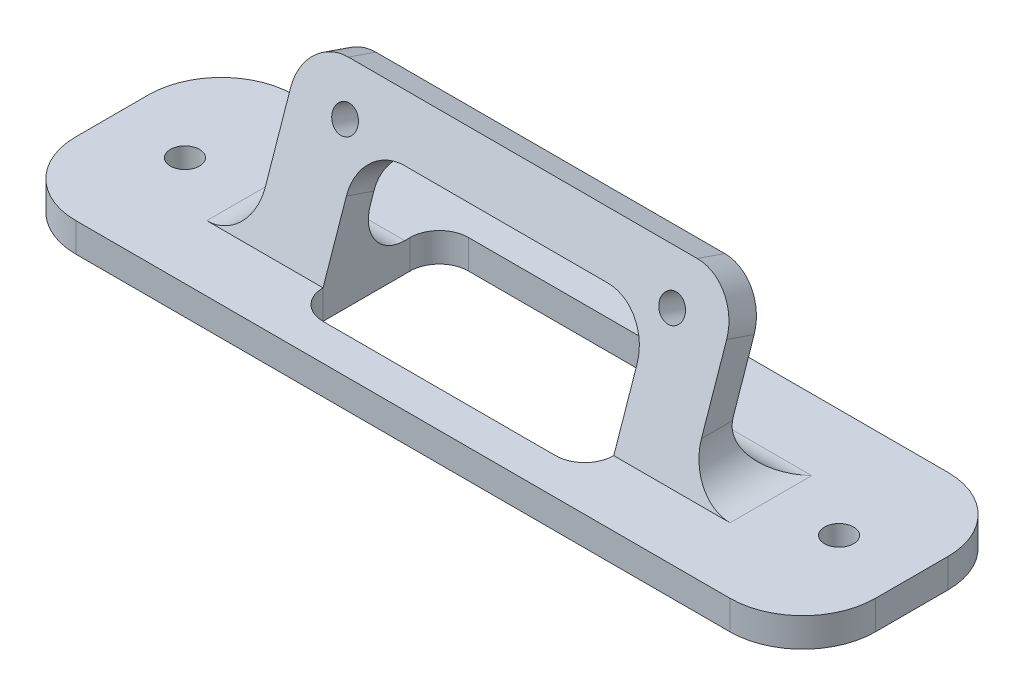
SolidWorks part; units mm, degrees
ref_plane "Plan de face" through (0, 0, 0) normal (0, 0, 1) x (1, 0, 0)
ref_plane "Plan de dessus" through (0, 0, 0) normal (0, 1, 0) x (1, 0, 0)
ref_plane "Plan de droite" through (0, 0, 0) normal (1, 0, 0) x (0, 0, -1)
sketch "Esquisse1" plane through (0, 0, 0) normal (0, 1, 0) x (1, 0, 0)
  line L0 (0, 38.2625) -> (0, -68.1123) construction
  line L1 (-45, 15) -> (45, 15)
  line L2 (-55, 5) -> (-55, -5)
  line L3 (-45, -15) -> (45, -15)
  line L4 (55, 5) -> (55, -5)
  line L6 (-124.7877, 0) -> (129.8356, 0) construction
  circle A0 centre (-45, 0) radius 2
  circle A1 centre (45, 0) radius 2
  arc A2 (-55, -5) -> (-45, -15) centre (-45, -5) ccw
  arc A3 (45, -15) -> (55, -5) centre (45, -5) ccw
  arc A4 (55, 5) -> (45, 15) centre (45, 5) ccw
  arc A5 (-45, 15) -> (-55, 5) centre (-45, 5) ccw
  point P15 (-55, -15)
  point P20 (55, 15)
  point P23 (-55, 15)
  dimension "D3" = 4
  dimension "D5" = 10
  dimension "D1" = 110
  dimension "D2" = 30
  dimension "D4" = 10
extrude "Boss.-Extru.1" add sketch "Esquisse1" along normal blind 4
sketch "Esquisse2" plane through (0, 0, 0) normal (1, 0, 0) x (0, 0, -1)
  line L0 (-6, 4) -> (1.4881, 25.7469)
  line L1 (-5, 4) -> (-15, 4) construction
  line L2 (1.4881, 25.7469) -> (5.2701, 24.4447)
  line L3 (5.2701, 24.4447) -> (-1.7695, 4)
  line L4 (-5, 4) -> (5, 4) construction
  line L5 (-1.7695, 4) -> (17.2566, 4) construction
  line L6 (-6, 4) -> (-1.7695, 4)
  point P12 (-15, 4)
  dimension "D1" = 4
  dimension "D2" = 71
  dimension "D3" = 23
  dimension "D4" = 9
extrude "Boss.-Extru.2" add sketch "Esquisse2" along normal blind 30 and the other way blind 30
sketch "Esquisse3" plane through (0, 2.271, 6.5954) normal (0, 0.3256, 0.9455) x (1, 0, 0)
  line L0 (0, 31.3543) -> (0, -19.6977) construction
  line L1 (-35.6324, 18.8287) -> (59.1643, 18.8287) construction
  line L2 (-30, 24.8287) -> (30, 24.8287) construction
  circle A0 centre (22.5, 18.8287) radius 1.75
  circle A1 centre (-22.5, 18.8287) radius 1.75
  dimension "D2" = 3.5
  dimension "D1" = 6
  dimension "D3" = 22.5
extrude "Enlèv. mat.-Extru.1" cut sketch "Esquisse3" against normal up to next
fillet "Congé1" radius 6 4 edges at (30, 4, 3.8848) (30, 25.0958, -3.3791) (-30, 25.0958, -3.3791) (-30, 4, 3.8848)
fillet "Congé2" radius 5 1 edges at (0, 4, 1.7695)
sketch "Esquisse4" plane through (0, 4, 0) normal (0, 1, 0) x (1, 0, 0)
  line L0 (0, 26.8591) -> (0, -31.313) construction
  line L1 (-20, 10) -> (20, 10)
  line L2 (-20, 10) -> (-20, -10)
  line L3 (-20, -10) -> (20, -10)
  line L4 (20, 10) -> (20, -10)
  line L5 (45, 15) -> (-45, 15) construction
  line L6 (-45, -15) -> (45, -15) construction
  dimension "D1" = 5
  dimension "D2" = 5
  dimension "D3" = 40
extrude "Enlèv. mat.-Extru.2" cut sketch "Esquisse4" against normal blind 22 and the other way blind 15
sketch "Esquisse5" plane through (0, 2.271, 6.5954) normal (0, 0.3256, 0.9455) x (1, 0, 0)
  line L0 (-24, 24.8287) -> (24, 24.8287) construction
  line L1 (-20, 17.693) -> (20, 17.693)
  line L2 (-20, 17.693) -> (-20, 24.8287)
  line L3 (-20, 24.8287) -> (20, 24.8287)
  line L4 (20, 17.693) -> (20, 24.8287)
extrude "Boss.-Extru.3" add sketch "Esquisse5" against normal up to surface (4 mm away) up to face at (22.5, 20.4262, -3.8865)
fillet "Congé4" radius 6 2 edges at (20, 18.3489, -1.056) (-20, 18.3489, -1.056)
fillet "Congé5" radius 4 4 edges at (-20, 2, -10) (-20, 2, 10) (20, 2, 10) (20, 2, -10)
